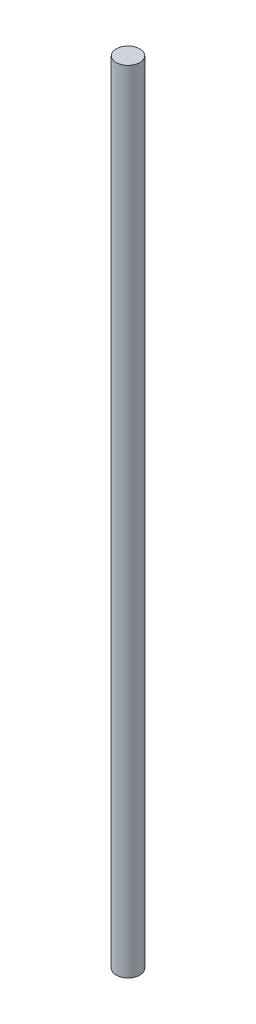
SolidWorks part; units mm, degrees
ref_plane "Plan de face" through (0, 0, 0) normal (0, 0, 1) x (1, 0, 0)
ref_plane "Plan de dessus" through (0, 0, 0) normal (0, 1, 0) x (1, 0, 0)
ref_plane "Plan de droite" through (0, 0, 0) normal (1, 0, 0) x (0, 0, -1)
sketch "Esquisse1" plane through (0, 0, 0) normal (0, 1, 0) x (1, 0, 0)
  circle A0 centre (0, 0) radius 1.5
  dimension "D1" = 3
extrude "Boss.-Extru.1" add sketch "Esquisse1" along normal blind 100
